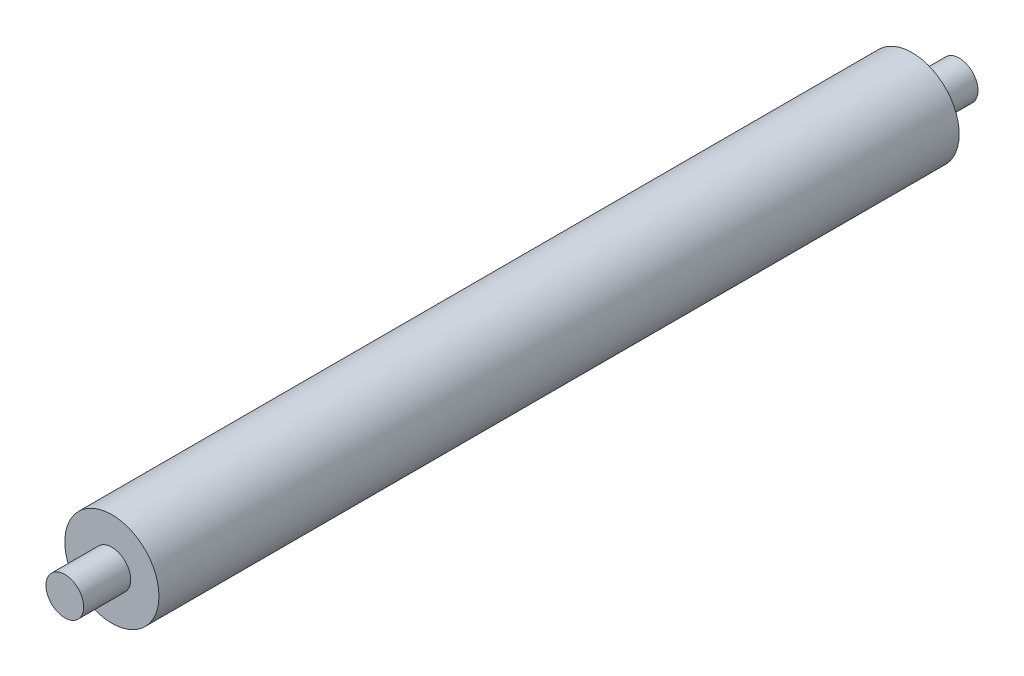
SolidWorks part; units mm, degrees
ref_plane "Front Plane" through (0, 0, 0) normal (0, 0, 1) x (1, 0, 0)
ref_plane "Top Plane" through (0, 0, 0) normal (0, 1, 0) x (1, 0, 0)
ref_plane "Right Plane" through (0, 0, 0) normal (1, 0, 0) x (0, 0, -1)
sketch "Sketch2" plane through (0, 0, 0) normal (1, 0, 0) x (0, 0, -1)
  line L0 (-47.5, 0) -> (47.5, 0)
  line L1 (-47.5, 0) -> (-47.5, 2)
  line L2 (-47.5, 2) -> (-42.5, 2)
  line L3 (-42.5, 2) -> (-42.5, 5)
  line L4 (-42.5, 5) -> (42.5, 5)
  line L5 (42.5, 5) -> (42.5, 2)
  line L6 (42.5, 2) -> (47.5, 2)
  line L7 (47.5, 2) -> (47.5, 0)
  dimension "D1" = 95
  dimension "D2" = 47.5
  dimension "D3" = 2
  dimension "D4" = 2
  dimension "D5" = 5
  dimension "D6" = 5
  dimension "D7" = 5
revolve "Revolve1" add sketch "Sketch2" angle 360 about L0
